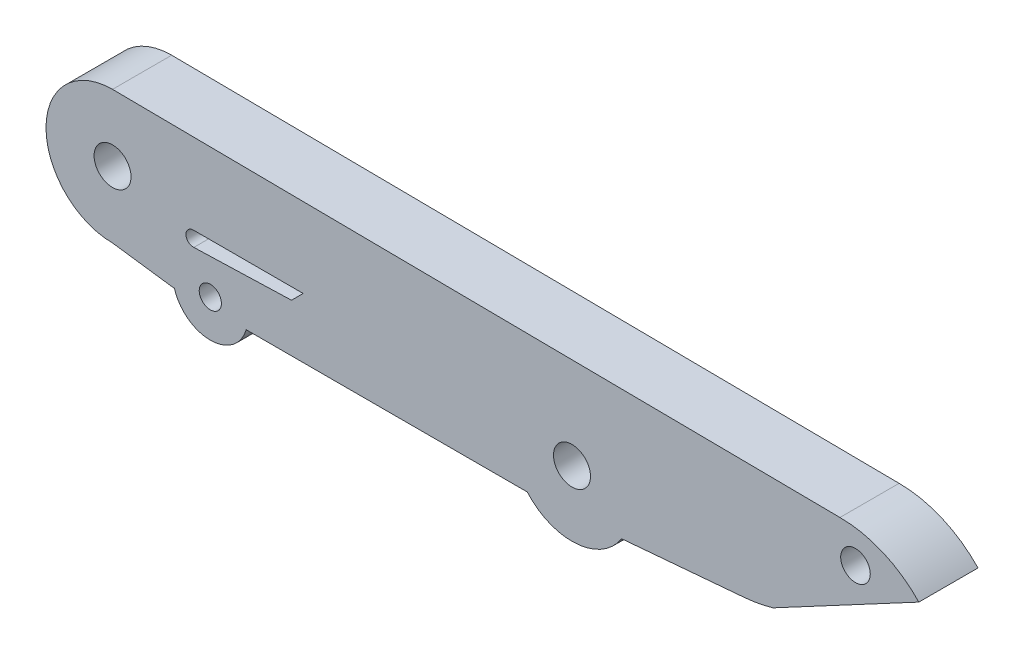
SolidWorks part; units mm, degrees
ref_plane "Front Plane" through (0, 0, 0) normal (0, 0, 1) x (1, 0, 0)
ref_plane "Top Plane" through (0, 0, 0) normal (0, 1, 0) x (1, 0, 0)
ref_plane "Right Plane" through (0, 0, 0) normal (1, 0, 0) x (0, 0, -1)
sketch "Sketch1" plane through (0, 0, 0) normal (0, 0, 1) x (1, 0, 0)
  line L0 (48.9235, -3.6305) -> (58.7811, 1.6353)
  line L1 (4.2542, 4.4026) -> (53.4455, 3.9242)
  line L2 (4.2542, -4.5974) -> (8.3469, -5.1552)
  line L3 (13.2922, -5.1552) -> (24.2922, -5.1552)
  line L4 (38.6853, -4.7034) -> (46.9804, -3.993)
  line L5 (9.719, -1.1064) -> (17.1467, -1.1064)
  line L6 (17.1467, -1.1064) -> (16.3559, -1.8973)
  line L7 (16.3559, -1.8973) -> (9.719, -2.1064)
  line L8 (24.2922, -5.1552) -> (32.3042, -5.1552)
  line L9 (8.3469, -5.1552) -> (8.4398, -5.1552)
  arc A0 (4.3417, 4.4018) -> (4.2542, -4.5974) centre (4.2542, -0.0974) ccw
  arc A1 (58.7811, 1.6353) -> (53.4455, 3.9242) centre (53.4455, -3.4392) ccw
  arc A2 (8.4398, -5.1552) -> (13.2922, -5.1552) centre (10.866, -4.4558) ccw
  circle A4 centre (10.866, -4.4558) radius 0.75
  arc A5 (32.3042, -5.1552) -> (38.6853, -4.7034) centre (35.3251, -2.5333) ccw
  circle A7 centre (4.2542, -0.0974) radius 1.25
  circle A9 centre (35.3251, -2.1054) radius 1.25
  circle A10 centre (54.4959, 1.6353) radius 1
  arc A11 (9.719, -1.1064) -> (9.7505, -2.1054) centre (9.719, -1.6064) ccw
  arc A12 (48.9235, -3.6305) -> (46.9804, -3.993) centre (46.127, 5.9706) cw
  dimension "D1" = 9
  dimension "D3" = 5.05
  dimension "D4" = 1.5
  dimension "D2" = 2.5
  dimension "D7" = 2
  dimension "D8" = 1
  dimension "D9" = 4
  dimension "D10" = 10
  dimension "D6" = 11
extrude "Boss-Extrude1" add sketch "Sketch1" along normal blind 4 contours A12 L0 A1 L1 A0 L2 L9 A2 L3 L8 A5 L4 A11 L5 L6 L7 A10 A9 A7 A4
